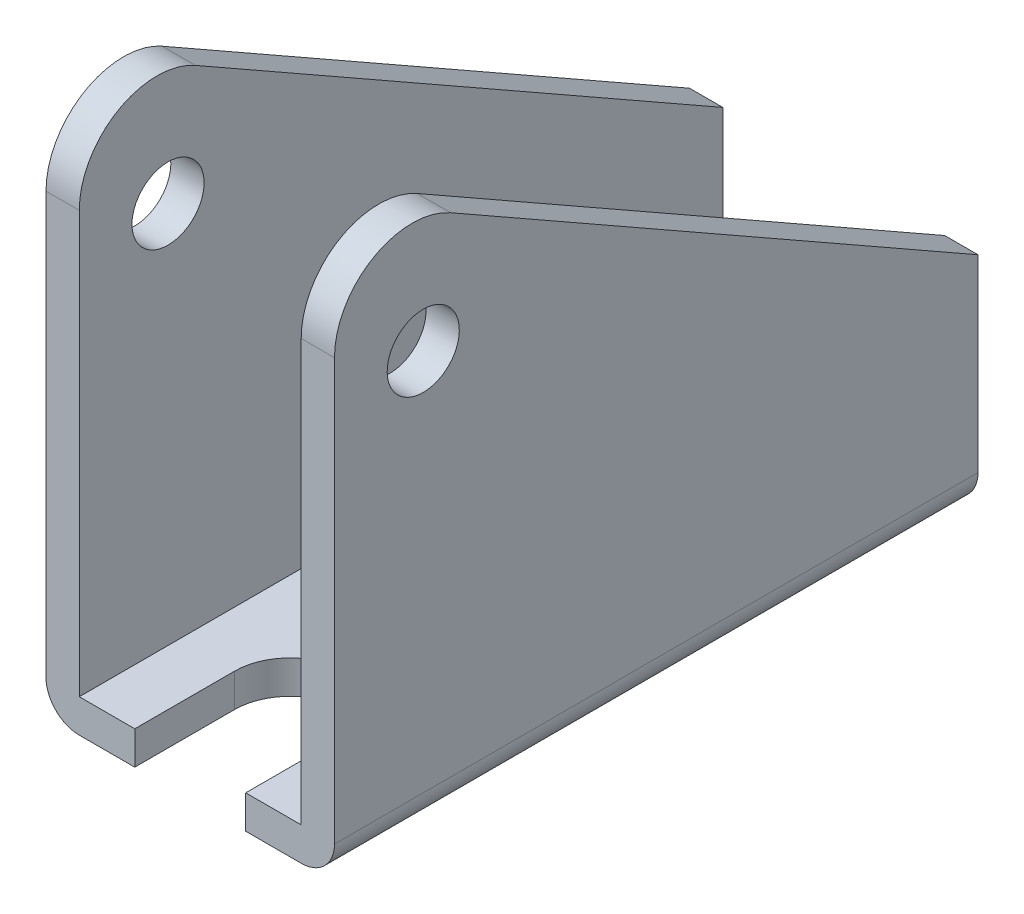
SolidWorks part; units mm, degrees
ref_plane "前视基准面" through (0, 0, 0) normal (0, 0, 1) x (1, 0, 0)
ref_plane "上视基准面" through (0, 0, 0) normal (0, 1, 0) x (1, 0, 0)
ref_plane "右视基准面" through (0, 0, 0) normal (1, 0, 0) x (0, 0, -1)
sketch "草图1" plane through (0, 0, 0) normal (0, 0, 1) x (1, 0, 0)
  line L0 (-25.3132, 0) -> (25.4167, 0) construction
  line L1 (0, 42.3624) -> (0, -24.8288) construction
  line L2 (-10, -20.7978) -> (-10, -72.7978)
  line L3 (-13, -20.7978) -> (-10, -20.7978)
  line L4 (-13, -20.7978) -> (-13, -75.7978)
  line L5 (-13, -75.7978) -> (13, -75.7978)
  line L6 (13, -20.7978) -> (13, -75.7978)
  line L7 (-10, -72.7978) -> (10, -72.7978)
  line L8 (10, -72.7978) -> (10, -20.7978)
  line L9 (10, -20.7978) -> (13, -20.7978)
  dimension "D1" = 3
  dimension "D2" = 3
  dimension "D3" = 55
  dimension "D4" = 26
extrude "凸台-拉伸1" add sketch "草图1" along normal blind 58
sketch "草图2" plane through (13, 0, 0) normal (1, 0, 0) x (0, 0, -1)
  line L0 (-58, -20.7978) -> (-58, -22.7978)
  line L1 (-58, -75.7978) -> (-58, -20.7978) construction
  line L2 (-58, -22.7978) -> (0, -55.7978)
  line L3 (0, -75.7978) -> (0, -20.7978) construction
  line L4 (0, -55.7978) -> (0, -20.7978)
  line L5 (0, -20.7978) -> (-58, -20.7978)
  line L6 (-58, -75.7978) -> (0, -75.7978) construction
  line L7 (-52.5204, -38.2978) -> (-24.1962, -38.2978) construction
  line L8 (-50, -38.7706) -> (-50, -78.2038) construction
  circle A0 centre (-50, -38.2978) radius 3.25
  dimension "D5" = 6.5
  dimension "D1" = 53
  dimension "D2" = 20
  dimension "D3" = 8
  dimension "D4" = 37.5
extrude "切除-拉伸1" cut sketch "草图2" against normal through all
fillet "圆角1" radius 7 2 edges at (11.5, -22.7978, 58) (-11.5, -22.7978, 58)
sketch "草图3" plane through (0, -72.7978, 0) normal (0, 1, 0) x (1, 0, 0)
  line L0 (-23.7429, -12) -> (24.7461, -12) construction
  line L1 (0, 24.9959) -> (0, -63.4851) construction
  line L2 (10, 0) -> (-10, 0) construction
  line L3 (5, -49) -> (5, -58)
  line L4 (10, -58) -> (-10, -58) construction
  line L5 (-5, -49) -> (-5, -58)
  line L6 (-5, -58) -> (5, -58)
  circle A0 centre (0, -12) radius 4.5
  arc A1 (5, -49) -> (-5, -49) centre (0, -49) ccw
  dimension "D1" = 9
  dimension "D3" = 10
  dimension "D2" = 12
  dimension "D4" = 9
extrude "切除-拉伸2" cut sketch "草图3" against normal through all
fillet "圆角2" radius 3 2 edges at (-13, -75.7978, 29) (13, -75.7978, 29)
